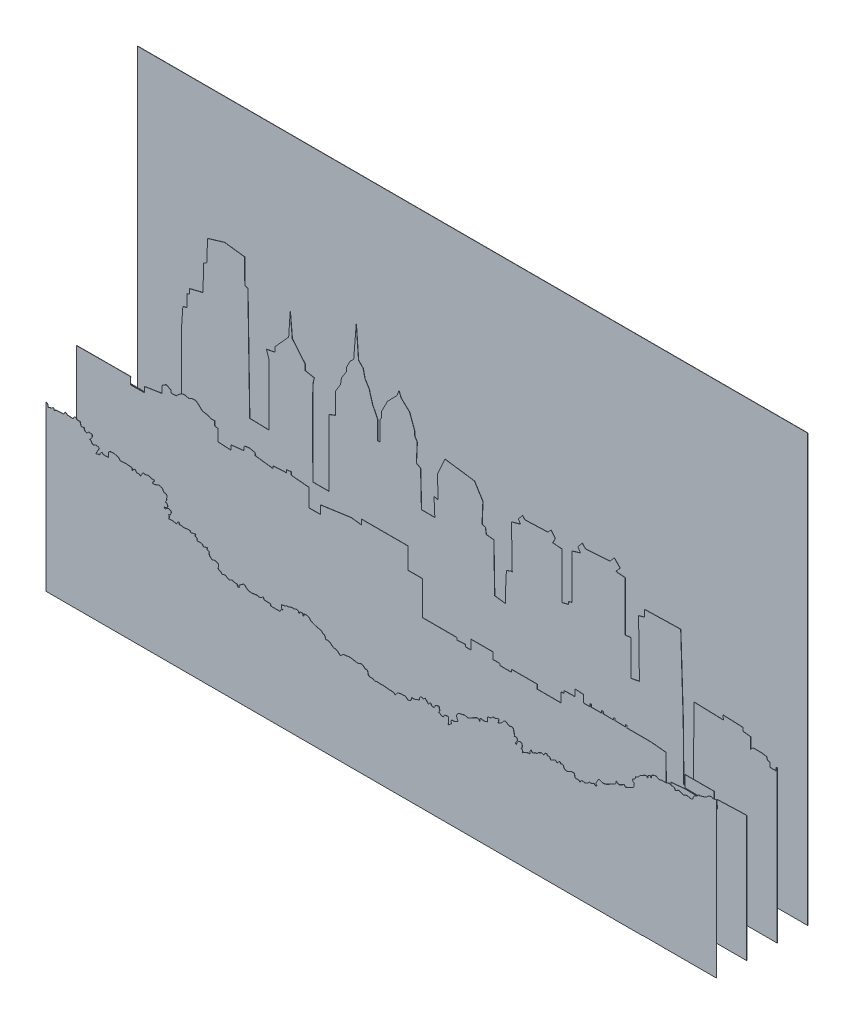
SolidWorks part; units mm, degrees
ref_plane "Front Plane" through (0, 0, 0) normal (0, 0, 1) x (1, 0, 0)
ref_plane "Top Plane" through (0, 0, 0) normal (0, 1, 0) x (1, 0, 0)
ref_plane "Right Plane" through (0, 0, 0) normal (1, 0, 0) x (0, 0, -1)
ref_plane "Plane2" through (0, 0, 12.7) normal (0, 0, 1) x (1, 0, 0)
ref_plane "Plane3" through (0, 0, 25.4) normal (0, 0, 1) x (1, 0, 0)
ref_plane "Plane4" through (0, 0, 38.1) normal (0, 0, 1) x (1, 0, 0)
sketch "Sketch2" plane through (0, 0, 12.7) normal (0, 0, 1) x (1, 0, 0)
  line L0 (279.4, -114.5341) -> (278.8098, -114.8294)
  line L1 (278.8098, -114.8294) -> (278.8098, -115.8829)
  line L2 (278.8098, -115.8829) -> (276.3531, -115.8829)
  line L3 (276.3531, -115.8829) -> (276.3531, -114.1271)
  line L4 (276.3531, -114.1271) -> (275.3003, -113.7759)
  line L5 (275.3003, -113.7759) -> (274.9493, -112.7224)
  line L6 (274.9493, -112.7224) -> (272.8436, -112.3712)
  line L7 (272.8436, -112.3712) -> (269.3341, -112.3712)
  line L8 (269.3341, -112.3712) -> (268.2813, -113.4247)
  line L9 (268.2813, -113.4247) -> (268.2813, -108.8596)
  line L10 (268.2813, -108.8596) -> (265.1227, -108.5084)
  line L11 (265.1227, -108.5084) -> (265.1227, -107.1038)
  line L12 (265.1227, -107.1038) -> (256.6999, -106.7526)
  line L13 (256.6999, -106.7526) -> (257.0508, -108.5084)
  line L14 (257.0508, -108.5084) -> (244.6514, -108.1264)
  line L15 (244.6514, -108.1264) -> (244.5456, -139.8764)
  line L16 (244.5456, -139.8764) -> (240.4181, -140.088)
  line L17 (240.4181, -140.088) -> (240.2053, -117.2875)
  line L18 (240.2053, -117.2875) -> (239.1524, -84.6293)
  line L19 (239.1524, -84.6293) -> (224.0616, -84.9805)
  line L20 (224.0616, -84.9805) -> (224.0616, -87.7898)
  line L21 (224.0616, -87.7898) -> (221.6049, -88.4921)
  line L22 (221.6049, -88.4921) -> (221.9559, -112.0201)
  line L23 (221.9559, -112.0201) -> (218.4463, -112.7224)
  line L24 (218.4463, -112.7224) -> (218.4463, -97.9735)
  line L25 (218.4463, -97.9735) -> (215.9897, -98.3247)
  line L26 (215.9897, -98.3247) -> (215.9897, -77.606)
  line L27 (215.9897, -77.606) -> (212.1293, -77.2549)
  line L28 (212.1293, -77.2549) -> (213.884, -75.1479)
  line L29 (213.884, -75.1479) -> (211.4274, -72.6897)
  line L30 (211.4274, -72.6897) -> (209.6726, -74.7967)
  line L31 (209.6726, -74.7967) -> (199.4951, -75.4991)
  line L32 (199.4951, -75.4991) -> (198.0913, -74.0944)
  line L33 (198.0913, -74.0944) -> (196.3365, -76.2014)
  line L34 (196.3365, -76.2014) -> (197.3894, -77.9572)
  line L35 (197.3894, -77.9572) -> (193.8799, -79.0107)
  line L36 (193.8799, -79.0107) -> (193.8799, -97.6224)
  line L37 (193.8799, -97.6224) -> (192.4761, -97.9735)
  line L38 (192.4761, -97.9735) -> (192.4761, -99.027)
  line L39 (192.4761, -99.027) -> (189.6685, -99.7294)
  line L40 (189.6685, -99.7294) -> (189.6685, -80.4153)
  line L41 (189.6685, -80.4153) -> (185.8081, -80.0642)
  line L42 (185.8081, -80.0642) -> (186.8609, -77.9572)
  line L43 (186.8609, -77.9572) -> (185.1061, -75.8502)
  line L44 (185.1061, -75.8502) -> (183.7023, -77.2549)
  line L45 (183.7023, -77.2549) -> (174.2267, -77.606)
  line L46 (174.2267, -77.606) -> (173.1738, -76.5525)
  line L47 (173.1738, -76.5525) -> (171.4191, -78.6595)
  line L48 (171.4191, -78.6595) -> (172.4719, -80.0642)
  line L49 (172.4719, -80.0642) -> (168.6115, -81.1177)
  line L50 (161.5925, -111.3178) -> (161.2415, -91.3014)
  line L51 (161.2415, -91.3014) -> (158.083, -90.9502)
  line L52 (158.083, -90.9502) -> (157.7321, -88.4921)
  line L53 (157.7321, -88.4921) -> (156.3282, -88.1409)
  line L54 (156.3282, -88.1409) -> (156.6792, -79.713)
  line L55 (156.6792, -79.713) -> (153.1697, -74.0944)
  line L56 (153.1697, -74.0944) -> (140.8864, -72.3386)
  line L57 (140.8864, -72.3386) -> (137.7279, -79.3618)
  line L58 (137.7279, -79.3618) -> (138.0788, -88.4921)
  line L59 (138.0788, -88.4921) -> (136.3241, -88.1409)
  line L60 (136.3241, -88.1409) -> (136.675, -95.5154)
  line L61 (136.675, -95.5154) -> (131.0598, -95.5154)
  line L62 (131.0598, -95.5154) -> (130.7089, -80.7665)
  line L63 (130.7089, -80.7665) -> (128.9541, -79.713)
  line L64 (128.9541, -79.713) -> (129.3051, -71.9874)
  line L65 (129.3051, -71.9874) -> (128.2522, -70.2316)
  line L66 (128.2522, -70.2316) -> (128.2522, -68.4758)
  line L67 (128.2522, -68.4758) -> (126.118, -62.7239)
  line L68 (126.118, -62.7239) -> (122.6255, -59.4431)
  line L69 (122.6255, -59.4431) -> (121.673, -57.2206)
  line L70 (121.673, -57.2206) -> (120.8823, -59.3455)
  line L71 (120.8823, -59.3455) -> (116.9105, -63.4647)
  line L72 (116.9105, -63.4647) -> (114.4764, -68.2272)
  line L73 (114.4764, -68.2272) -> (114.4764, -70.4497)
  line L74 (114.4764, -70.4497) -> (113.8633, -71.6363)
  line L75 (113.8633, -71.6363) -> (113.8633, -79.713)
  line L76 (113.8633, -79.713) -> (112.8104, -79.713)
  line L77 (112.8104, -79.713) -> (112.8104, -71.9874)
  line L78 (112.8104, -71.9874) -> (110.7047, -67.7734)
  line L79 (110.7047, -67.7734) -> (109.6519, -64.2618)
  line L80 (109.6519, -64.2618) -> (109.3009, -62.8571)
  line L81 (109.3009, -62.8571) -> (108.2481, -61.1013)
  line L82 (108.2481, -61.1013) -> (107.5462, -60.0479)
  line L83 (107.5462, -60.0479) -> (106.7505, -56.5855)
  line L84 (106.7505, -56.5855) -> (104.8456, -54.6806)
  line L85 (104.8456, -54.6806) -> (103.8931, -42.0864)
  line L86 (103.8931, -42.0864) -> (102.8347, -55.3156)
  line L87 (102.8347, -55.3156) -> (101.353, -56.6914)
  line L88 (101.353, -56.6914) -> (99.8253, -59.6967)
  line L89 (99.8253, -59.6967) -> (99.7655, -61.348)
  line L90 (99.7655, -61.348) -> (97.7196, -64.613)
  line L91 (97.7196, -64.613) -> (97.3686, -67.0711)
  line L92 (97.3686, -67.0711) -> (95.2629, -70.5828)
  line L93 (95.2629, -70.5828) -> (95.2629, -73.0409)
  line L94 (95.2629, -73.0409) -> (95.2629, -79.3618)
  line L95 (95.2629, -79.3618) -> (92.4554, -80.4153)
  line L96 (92.4554, -80.4153) -> (92.4554, -108.1573)
  line L97 (92.4554, -108.1573) -> (85.7873, -108.1573)
  line L98 (86.3247, -70.238) -> (82.6287, -69.5293)
  line L99 (82.6287, -69.5293) -> (82.6206, -67.1689)
  line L100 (82.6206, -67.1689) -> (77.223, -60.713)
  line L101 (77.223, -60.713) -> (76.3764, -51.188)
  line L102 (76.3764, -51.188) -> (75.7414, -60.8189)
  line L103 (75.7414, -60.8189) -> (70.0264, -67.1689)
  line L104 (70.0264, -67.1689) -> (69.9206, -69.1797)
  line L105 (69.9206, -69.1797) -> (66.4851, -69.8804)
  line L106 (66.4851, -69.8804) -> (67.5379, -73.0409)
  line L107 (59.4661, -98.3247) -> (58.7022, -51.7172)
  line L108 (58.7022, -51.7172) -> (57.4322, -51.3997)
  line L109 (57.4322, -51.3997) -> (57.3604, -41.085)
  line L110 (57.3604, -41.085) -> (48.9376, -40.0315)
  line L111 (48.9376, -40.0315) -> (41.9186, -42.1385)
  line L112 (41.9186, -42.1385) -> (41.5676, -51.2687)
  line L113 (41.5676, -51.2687) -> (40.1814, -51.823)
  line L114 (40.1814, -51.823) -> (40.0755, -62.6181)
  line L115 (40.0755, -62.6181) -> (34.4664, -63.9939)
  line L116 (34.4664, -63.9939) -> (34.4664, -66.0047)
  line L117 (34.4664, -66.0047) -> (33.3022, -66.4281)
  line L118 (33.3022, -66.4281) -> (33.4081, -71.4022)
  line L119 (33.4081, -71.4022) -> (31.6089, -71.8255)
  line L120 (31.6089, -71.8255) -> (31.0391, -80.0642)
  line L121 (31.0391, -80.0642) -> (31.0391, -110.9666)
  line L122 (31.0391, -110.9666) -> (0, -110.4702)
  line L123 (0, -110.4702) -> (0, -177.8007)
  line L124 (0, -177.8007) -> (279.4, -177.8007)
  line L125 (279.4, -177.8007) -> (279.4, -114.5341)
  spline S0 degree 2 poles (168.6115, -81.1177) (168.817, -97.9614) (168.9471, -98.9799) knots 50 50 50 51 51 51
  spline S3 degree 2 poles (168.9471, -98.9799) (168.7315, -98.8503) (166.5058, -99.7294) knots 53 53 53 54 54 54
  spline S4 degree 2 poles (166.5058, -99.7294) (165.8655, -111.1017) (166.1152, -111.9622) knots 54 54 54 55 55 55
  spline S7 degree 2 poles (166.1152, -111.9622) (165.5917, -111.7562) (161.5925, -111.3178) knots 57 57 57 58 58 58
  spline S8 degree 2 poles (85.7873, -108.1573) (85.6534, -74.3035) (85.7873, -73.0409) knots 106 106 106 107 107 107
  spline S9 degree 3 poles (85.7873, -73.0409) (85.9115, -71.8699) (86.436, -70.2546) (86.3247, -70.238) knots 107 107 107 107 108 108 108 108
  spline S10 degree 2 poles (67.5379, -73.0409) (67.5839, -96.8299) (67.5569, -98.5132) knots 117 117 117 118 118 118
  spline S11 degree 2 poles (67.5569, -98.5132) (67.5678, -98.5381) (59.4661, -98.3247) knots 118 118 118 119 119 119
sketch "Sketch3" plane through (0, 0, 25.4) normal (0, 0, 1) x (1, 0, 0)
  line L0 (279.4, -125.4381) -> (278.7297, -125.3772)
  line L1 (278.7297, -125.3772) -> (266.9822, -125.8005)
  line L2 (266.9822, -125.8005) -> (267.1939, -129.1872)
  line L3 (267.1939, -129.1872) -> (261.4789, -128.9755)
  line L4 (261.4789, -128.9755) -> (261.4789, -128.4464)
  line L5 (261.4789, -128.4464) -> (265.818, -128.3406)
  line L6 (265.818, -128.3406) -> (265.818, -123.4722)
  line L7 (265.818, -123.4722) -> (253.753, -123.4722)
  line L8 (253.753, -123.4722) -> (253.753, -128.2347)
  line L9 (253.753, -128.2347) -> (258.9389, -128.3406)
  line L10 (258.9389, -128.3406) -> (258.833, -128.7639)
  line L11 (258.833, -128.7639) -> (253.6472, -128.6581)
  line L12 (253.6472, -128.6581) -> (247.8264, -129.1872)
  line L13 (247.8264, -129.1872) -> (247.8264, -141.6755)
  line L14 (247.8264, -141.6755) -> (245.8155, -140.8289)
  line L15 (245.8155, -140.8289) -> (245.7097, -119.4505)
  line L16 (245.7097, -119.4505) -> (239.4655, -118.8156)
  line L17 (239.4655, -118.8156) -> (229.4113, -118.8156)
  line L18 (229.4113, -118.8156) -> (229.4113, -117.863)
  line L19 (229.4113, -117.863) -> (228.7763, -117.863)
  line L20 (228.7763, -117.863) -> (228.7763, -118.7097)
  line L21 (228.7763, -118.7097) -> (224.4372, -118.6039)
  line L22 (224.4372, -118.6039) -> (224.4372, -117.863)
  line L23 (224.4372, -117.863) -> (223.9081, -117.863)
  line L24 (223.9081, -117.863) -> (223.9081, -118.7097)
  line L25 (223.9081, -118.7097) -> (219.5689, -118.6039)
  line L26 (219.5689, -118.6039) -> (219.5689, -117.7572)
  line L27 (219.5689, -117.7572) -> (218.828, -117.7572)
  line L28 (218.828, -117.7572) -> (218.828, -118.7097)
  line L29 (218.828, -118.7097) -> (214.4889, -118.7097)
  line L30 (214.4889, -118.7097) -> (214.4889, -117.6514)
  line L31 (214.4889, -117.6514) -> (214.0655, -117.6514)
  line L32 (214.0655, -117.6514) -> (214.0655, -118.8156)
  line L33 (214.0655, -118.8156) -> (211.3138, -118.8156)
  line L34 (211.3138, -118.8156) -> (211.3138, -115.7464)
  line L35 (211.3138, -115.7464) -> (207.8214, -115.5347)
  line L36 (207.8214, -115.5347) -> (207.8214, -118.2864)
  line L37 (207.8214, -118.2864) -> (203.2706, -118.3922)
  line L38 (203.2706, -118.3922) -> (203.2706, -119.4505)
  line L39 (203.2706, -119.4505) -> (202.0005, -119.4505)
  line L40 (202.0005, -119.4505) -> (202.0005, -123.4722)
  line L41 (202.0005, -123.4722) -> (192.0522, -123.4722)
  line L42 (192.0522, -123.4722) -> (192.0522, -121.673)
  line L43 (192.0522, -121.673) -> (181.363, -121.673)
  line L44 (181.363, -121.673) -> (181.363, -122.7314)
  line L45 (181.363, -122.7314) -> (176.4947, -122.7314)
  line L46 (176.4947, -122.7314) -> (176.4947, -121.9906)
  line L47 (176.4947, -121.9906) -> (173.5314, -121.9906)
  line L48 (173.5314, -121.9906) -> (173.5314, -119.2389)
  line L49 (173.5314, -119.2389) -> (164.4297, -119.2389)
  line L50 (164.4297, -119.2389) -> (164.4297, -123.1547)
  line L51 (164.4297, -123.1547) -> (162.2072, -123.1547)
  line L52 (162.2072, -123.1547) -> (161.9956, -122.3081)
  line L53 (161.9956, -122.3081) -> (158.6089, -122.5197)
  line L54 (158.6089, -122.5197) -> (158.6089, -121.5672)
  line L55 (158.6089, -121.5672) -> (150.5655, -121.5672)
  line L56 (150.5655, -121.5672) -> (144.2155, -121.5672)
  line L57 (144.2155, -121.5672) -> (144.2155, -107.4914)
  line L58 (144.2155, -107.4914) -> (138.1831, -107.4914)
  line L59 (138.1831, -107.4914) -> (138.1831, -98.7072)
  line L60 (138.1831, -98.7072) -> (135.2197, -98.7072)
  line L61 (135.2197, -98.7072) -> (118.7097, -98.7072)
  line L62 (118.7097, -98.7072) -> (118.7097, -100.8239)
  line L63 (118.7097, -100.8239) -> (114.5822, -100.2947)
  line L64 (114.5822, -100.2947) -> (101.7764, -102.0939)
  line L65 (101.7764, -102.0939) -> (101.7764, -105.5864)
  line L66 (101.7764, -105.5864) -> (96.8022, -105.5864)
  line L67 (96.8022, -105.5864) -> (96.8022, -98.1781)
  line L68 (96.8022, -98.1781) -> (89.8172, -97.5431)
  line L69 (89.8172, -97.5431) -> (89.4997, -97.4372)
  line L70 (89.4997, -97.4372) -> (89.4997, -96.273)
  line L71 (89.4997, -96.273) -> (87.4889, -96.4847)
  line L72 (87.4889, -96.4847) -> (87.4889, -97.6489)
  line L73 (87.4889, -97.6489) -> (86.6422, -97.6489)
  line L74 (86.6422, -97.6489) -> (81.9855, -97.9664)
  line L75 (81.9855, -97.9664) -> (81.9855, -98.9189)
  line L76 (81.9855, -98.9189) -> (74.4714, -97.9664)
  line L77 (74.4714, -97.9664) -> (74.3655, -96.9081)
  line L78 (74.3655, -96.9081) -> (72.0372, -96.3789)
  line L79 (72.0372, -96.3789) -> (69.9206, -96.6964)
  line L80 (69.9206, -96.6964) -> (69.8147, -98.4956)
  line L81 (69.8147, -98.4956) -> (64.3113, -99.1306)
  line L82 (64.3113, -99.1306) -> (64.3113, -101.0355)
  line L83 (64.3113, -101.0355) -> (58.9139, -100.7181)
  line L84 (58.9139, -100.7181) -> (58.9139, -95.9556)
  line L85 (58.9139, -95.9556) -> (57.538, -95.638)
  line L86 (57.538, -95.638) -> (57.538, -93.8389)
  line L87 (57.538, -93.8389) -> (55.8447, -93.8389)
  line L88 (55.8447, -93.8389) -> (54.6805, -93.2039)
  line L89 (41.5572, -92.7806) -> (39.3347, -92.8864)
  line L90 (39.3347, -92.8864) -> (39.3347, -91.8281)
  line L91 (39.3347, -91.8281) -> (37.3239, -90.8755)
  line L92 (37.3239, -90.8755) -> (35.5247, -92.0397)
  line L93 (35.5247, -92.0397) -> (35.5247, -94.8972)
  line L94 (35.5247, -94.8972) -> (28.2222, -96.0614)
  line L95 (28.2222, -96.0614) -> (28.2222, -98.2839)
  line L96 (22.5072, -95.3206) -> (0, -95.4233)
  line L97 (0, -95.4233) -> (0, -177.8007)
  line L98 (0, -177.8007) -> (279.4, -177.8007)
  line L99 (279.4, -177.8007) -> (279.4, -125.4381)
  spline S0 degree 2 poles (54.6805, -93.2039) (53.3175, -93.1351) (52.4581, -92.7806) knots 89 89 89 90 90 90
  spline S1 degree 3 poles (52.4581, -92.7806) (51.5986, -92.426) (50.4766, -90.4502) (49.1772, -90.4522) knots 90 90 90 90 91 91 91 91
  spline S2 degree 2 poles (49.1772, -90.4522) (47.8778, -90.4542) (46.8489, -91.0872) knots 91 91 91 92 92 92
  spline S3 degree 2 poles (46.8489, -91.0872) (46.5744, -91.0746) (45.1555, -90.7697) knots 92 92 92 93 93 93
  spline S4 degree 2 poles (45.1555, -90.7697) (43.7367, -90.4648) (41.5572, -92.7806) knots 93 93 93 94 94 94
  spline S5 degree 2 poles (28.2222, -98.2839) (25.84, -98.3101) (22.4437, -98.3474) knots 101 101 101 102 102 102
  spline S6 degree 2 poles (22.4437, -98.3474) (22.3941, -97.9943) (22.5072, -95.3206) knots 102 102 102 103 103 103
sketch "Sketch4" plane through (0, 0, 38.1) normal (0, 0, 1) x (1, 0, 0)
  spline S0 degree 3 poles (277.6535, -113.4166) (277.8489, -113.5395) (278.1269, -113.5979) (278.3595, -113.579) (278.7103, -113.5503) (279.0536, -113.4293) (279.4, -113.3475) knots 344 344 344 344 345 345 345 346 346 346 346
  spline S1 degree 3 poles (275.0784, -114.5842) (275.7056, -114.1861) (276.092, -113.4532) (276.9622, -113.3634) (277.2245, -113.3364) (277.4013, -113.258) (277.6535, -113.4166) knots 342 342 342 342 343 343 343 344 344 344 344
  spline S2 degree 3 poles (274.832, -114.7215) (274.9201, -114.6961) (274.9989, -114.6346) (275.0784, -114.5842) knots 341 341 341 341 342 342 342 342
  spline S3 degree 3 poles (270.7793, -116.2787) (271.0483, -116.1877) (271.3769, -116.0603) (271.5159, -115.8445) (271.7585, -115.4676) (272.0293, -115.3147) (272.4622, -115.3515) (272.6253, -115.3654) (272.7982, -115.2898) (272.9637, -115.2444) (273.5874, -115.0735) (274.2107, -114.9007) (274.832, -114.7215) knots 337 337 337 337 338 338 338 339 339 339 340 340 340 341 341 341 341
  spline S4 degree 3 poles (269.4172, -118.1302) (269.6583, -117.9244) (269.7833, -117.5329) (269.8631, -117.199) (269.9868, -116.6819) (270.3079, -116.4381) (270.7793, -116.2787) knots 335 335 335 335 336 336 336 337 337 337 337
  spline S5 degree 3 poles (268.5118, -118.2598) (268.7894, -118.3381) (269.2171, -118.3009) (269.4172, -118.1302) knots 334 334 334 334 335 335 335 335
  spline S6 degree 3 poles (266.0554, -118.4191) (266.8481, -117.8055) (267.6618, -118.0199) (268.5118, -118.2598) knots 333 333 333 333 334 334 334 334
  spline S7 degree 3 poles (262.9789, -118.1896) (263.253, -118.0471) (263.5694, -117.78) (263.815, -117.8292) (264.4236, -117.9511) (264.9992, -118.2318) (265.5954, -118.4263) (265.7366, -118.4724) (265.9567, -118.4955) (266.0554, -118.4191) knots 330 330 330 330 331 331 331 332 332 332 333 333 333 333
  spline S8 degree 3 poles (262.3413, -118.5859) (262.5775, -118.4374) (262.7702, -118.2981) (262.9789, -118.1896) knots 329 329 329 329 330 330 330 330
  spline S9 degree 3 poles (260.8926, -117.5731) (261.6696, -117.4571) (262.0818, -117.8716) (262.3413, -118.5859) knots 328 328 328 328 329 329 329 329
  spline S10 degree 3 poles (260.4651, -117.4413) (260.6112, -117.4746) (260.7599, -117.5929) (260.8926, -117.5731) knots 327 327 327 327 328 328 328 328
  spline S11 degree 3 poles (259.6163, -117.2905) (259.8843, -117.2469) (260.1829, -117.3768) (260.4651, -117.4413) knots 326 326 326 326 327 327 327 327
  spline S12 degree 3 poles (256.445, -117.7031) (256.5179, -117.6462) (256.6827, -117.7132) (256.8047, -117.7118) (257.339, -117.7055) (257.8803, -117.7451) (258.4052, -117.6704) (258.8184, -117.6116) (259.2028, -117.3578) (259.6163, -117.2905) knots 323 323 323 323 324 324 324 325 325 325 326 326 326 326
  spline S13 degree 3 poles (254.4694, -117.5321) (255.0845, -117.7956) (255.7303, -118.2616) (256.445, -117.7031) knots 322 322 322 322 323 323 323 323
  spline S14 degree 3 poles (252.611, -117.9257) (252.8177, -117.7632) (253.1083, -117.7128) (253.3458, -117.5827) (253.7187, -117.3783) (254.0435, -117.3497) (254.4694, -117.5321) knots 320 320 320 320 321 321 321 322 322 322 322
  spline S15 degree 3 poles (252.4034, -118.446) (252.35, -118.3167) (252.4783, -118.0302) (252.611, -117.9257) knots 319 319 319 319 320 320 320 320
  spline S16 degree 3 poles (252.1662, -119.0873) (252.481, -118.9229) (252.5297, -118.7524) (252.4034, -118.446) knots 318 318 318 318 319 319 319 319
  spline S17 degree 3 poles (251.8468, -118.4123) (251.9592, -118.6497) (252.0578, -118.8582) (252.1662, -119.0873) knots 317 317 317 317 318 318 318 318
  spline S18 degree 3 poles (251.2681, -118.6778) (251.4583, -118.6085) (251.6376, -118.5095) (251.8468, -118.4123) knots 316 316 316 316 317 317 317 317
  spline S19 degree 3 poles (250.9507, -119.4467) (250.6904, -119.0283) (250.8748, -118.8212) (251.2681, -118.6778) knots 315 315 315 315 316 316 316 316
  spline S20 degree 3 poles (250.9241, -119.7554) (250.9355, -119.6509) (250.9943, -119.517) (250.9507, -119.4467) knots 314 314 314 314 315 315 315 315
  spline S21 degree 3 poles (250.6, -119.648) (250.6908, -119.7093) (250.8149, -119.7213) (250.9241, -119.7554) knots 313 313 313 313 314 314 314 314
  spline S22 degree 3 poles (249.1495, -119.643) (249.4659, -119.4838) (249.8121, -119.353) (250.1589, -119.3012) (250.2845, -119.2824) (250.441, -119.5406) (250.6, -119.648) knots 311 311 311 311 312 312 312 313 313 313 313
  spline S23 degree 3 poles (248.277, -120.2105) (248.5931, -120.0869) (248.8411, -119.7982) (249.1495, -119.643) knots 310 310 310 310 311 311 311 311
  spline S24 degree 3 poles (247.0043, -121.2797) (247.2666, -120.7246) (247.7198, -120.4283) (248.277, -120.2105) knots 309 309 309 309 310 310 310 310
  spline S25 degree 3 poles (245.6518, -121.9401) (246.0428, -121.7742) (246.4105, -121.6234) (246.7729, -121.4608) (246.8609, -121.4213) (246.9666, -121.3595) (247.0043, -121.2797) knots 307 307 307 307 308 308 308 309 309 309 309
  spline S26 degree 3 poles (244.8082, -123.1288) (245.3596, -122.9278) (245.7205, -122.584) (245.6518, -121.9401) knots 306 306 306 306 307 307 307 307
  spline S27 degree 3 poles (244.813, -124.2751) (244.6928, -124.1824) (244.6668, -123.9741) (244.5822, -123.827) (244.3974, -123.5058) (244.4325, -123.2658) (244.8082, -123.1288) knots 304 304 304 304 305 305 305 306 306 306 306
  spline S28 degree 3 poles (245.4544, -124.6041) (245.2673, -124.5125) (245.0128, -124.4292) (244.813, -124.2751) knots 303 303 303 303 304 304 304 304
  spline S29 degree 3 poles (244.8273, -126.1757) (244.9105, -126.1336) (245, -125.998) (244.9969, -125.909) (244.9772, -125.3441) (245.0335, -124.8208) (245.4544, -124.6041) knots 301 301 301 301 302 302 302 303 303 303 303
  spline S30 degree 3 poles (241.2193, -127.42) (241.3384, -127.8726) (241.6147, -127.7636) (241.8846, -127.633) (242.8698, -127.1561) (243.8509, -126.6704) (244.8273, -126.1757) knots 299 299 299 299 300 300 300 301 301 301 301
  spline S31 degree 3 poles (240.9015, -127.1409) (241.0029, -127.2255) (241.1884, -127.3024) (241.2193, -127.42) knots 298 298 298 298 299 299 299 299
  spline S32 degree 3 poles (239.018, -128.1348) (239.6711, -127.8682) (240.2755, -127.4824) (240.9015, -127.1409) knots 297 297 297 297 298 298 298 298
  spline S33 degree 3 poles (238.211, -127.876) (238.4786, -127.9842) (238.8168, -128.217) (239.018, -128.1348) knots 296 296 296 296 297 297 297 297
  spline S34 degree 3 poles (237.5604, -127.5373) (237.8561, -127.6932) (238.0267, -127.8014) (238.211, -127.876) knots 295 295 295 295 296 296 296 296
  spline S35 degree 3 poles (236.8231, -128.9905) (237.399, -128.8532) (237.7507, -128.3385) (237.5604, -127.5373) knots 294 294 294 294 295 295 295 295
  spline S36 degree 3 poles (233.3709, -130.7444) (233.7902, -130.5983) (234.1883, -130.3532) (234.5734, -130.1692) (235.3349, -129.8053) (235.9588, -129.1966) (236.8231, -128.9905) knots 292 292 292 292 293 293 293 294 294 294 294
  spline S37 degree 3 poles (231.4864, -130.8083) (232.1228, -131.0503) (232.7575, -130.9582) (233.3709, -130.7444) knots 291 291 291 291 292 292 292 292
  spline S38 degree 3 poles (230.68, -130.4997) (230.9555, -130.5793) (231.2172, -130.7059) (231.4864, -130.8083) knots 290 290 290 290 291 291 291 291
  spline S39 degree 3 poles (230.0889, -130.8779) (230.2223, -130.6235) (230.3599, -130.4072) (230.68, -130.4997) knots 289 289 289 289 290 290 290 290
  spline S40 degree 3 poles (229.1706, -132.5056) (229.508, -131.912) (229.8135, -131.4028) (230.0889, -130.8779) knots 288 288 288 288 289 289 289 289
  spline S41 degree 3 poles (229.6523, -133.2341) (229.4398, -132.9127) (229.2747, -132.6631) (229.1706, -132.5056) knots 287 287 287 287 288 288 288 288
  spline S42 degree 3 poles (228.8707, -133.5326) (229.1392, -133.4301) (229.4104, -133.3265) (229.6523, -133.2341) knots 286 286 286 286 287 287 287 287
  spline S43 degree 3 poles (226.7528, -133.4715) (227.1672, -133.6316) (227.4869, -133.4509) (227.8078, -133.2446) (228.363, -132.8878) (228.5286, -132.928) (228.8707, -133.5326) knots 284 284 284 284 285 285 285 286 286 286 286
  spline S44 degree 3 poles (226.3151, -133.5144) (226.3271, -133.4644) (226.6248, -133.4221) (226.7528, -133.4715) knots 283 283 283 283 284 284 284 284
  spline S45 degree 3 poles (225.041, -134.4994) (225.4742, -134.1934) (226.1533, -134.1901) (226.3151, -133.5144) knots 282 282 282 282 283 283 283 283
  spline S46 degree 3 poles (222.5676, -135.4002) (223.2255, -134.3727) (223.0714, -134.4287) (224.2952, -134.607) (224.5381, -134.6424) (224.8564, -134.6298) (225.041, -134.4994) knots 280 280 280 280 281 281 281 282 282 282 282
  spline S47 degree 3 poles (222.06, -135.0287) (222.2409, -135.1288) (222.3974, -135.2729) (222.5676, -135.4002) knots 279 279 279 279 280 280 280 280
  spline S48 degree 3 poles (221.5471, -134.8559) (221.646, -134.7942) (221.8994, -134.9397) (222.06, -135.0287) knots 278 278 278 278 279 279 279 279
  spline S49 degree 3 poles (220.499, -134.7876) (220.7008, -134.9685) (221.0718, -135.152) (221.5471, -134.8559) knots 277 277 277 277 278 278 278 278
  spline S50 degree 3 poles (220.0677, -133.3895) (220.2455, -133.792) (220.3385, -134.2321) (220.499, -134.7876) knots 276 276 276 276 277 277 277 277
  spline S51 degree 3 poles (218.7104, -133.4714) (218.9427, -133.3749) (219.2183, -133.3697) (219.4763, -133.3521) (219.68, -133.3382) (220.0303, -133.3048) (220.0677, -133.3895) knots 274 274 274 274 275 275 275 276 276 276 276
  spline S52 degree 3 poles (215.8081, -133.4785) (215.8534, -133.6598) (216.0616, -133.8455) (216.2416, -133.937) (216.4972, -134.0671) (216.7921, -134.1395) (217.0783, -134.1818) (217.2314, -134.2044) (217.414, -134.138) (217.5613, -134.0664) (217.9493, -133.8777) (218.3136, -133.6362) (218.7104, -133.4714) knots 270 270 270 270 271 271 271 272 272 272 273 273 273 274 274 274 274
  spline S53 degree 3 poles (214.5018, -132.8058) (215.274, -132.4315) (215.5875, -132.5959) (215.8081, -133.4785) knots 269 269 269 269 270 270 270 270
  spline S54 degree 3 poles (214.2119, -132.1961) (214.3086, -132.3994) (214.4053, -132.6028) (214.5018, -132.8058) knots 268 268 268 268 269 269 269 269
  spline S55 degree 3 poles (213.4819, -132.6879) (213.6991, -132.4946) (213.9661, -132.3573) (214.2119, -132.1961) knots 267 267 267 267 268 268 268 268
  spline S56 degree 3 poles (213.1194, -133.25) (213.2571, -133.0289) (213.3345, -132.8192) (213.4819, -132.6879) knots 266 266 266 266 267 267 267 267
  spline S57 degree 3 poles (210.2547, -133.56) (210.642, -133.3794) (211.0618, -133.2508) (211.4012, -133.0092) (211.8822, -132.6669) (212.389, -132.6232) (212.8181, -132.9985) (212.9105, -133.0793) (213.0066, -133.156) (213.1194, -133.25) knots 263 263 263 263 264 264 264 265 265 265 266 266 266 266
  spline S58 degree 3 poles (209.0434, -132.7656) (209.7372, -132.4177) (210.0428, -132.5962) (210.2547, -133.56) knots 262 262 262 262 263 263 263 263
  spline S59 degree 3 poles (207.7564, -132.648) (207.9424, -132.2832) (208.2435, -132.0391) (208.6142, -132.1227) (208.7944, -132.1634) (208.8998, -132.5362) (209.0434, -132.7656) knots 260 260 260 260 261 261 261 262 262 262 262
  spline S60 degree 3 poles (206.5407, -132.8531) (206.8202, -132.951) (207.0893, -133.1131) (207.357, -133.1109) (207.4938, -133.1098) (207.6627, -132.8318) (207.7564, -132.648) knots 258 258 258 258 259 259 259 260 260 260 260
  spline S61 degree 3 poles (205.2076, -133.4614) (205.6697, -133.2258) (206.1511, -133.028) (206.5407, -132.8531) knots 257 257 257 257 258 258 258 258
  spline S62 degree 3 poles (204.7905, -133.8547) (204.9262, -133.7189) (205.0442, -133.5448) (205.2076, -133.4614) knots 256 256 256 256 257 257 257 257
  spline S63 degree 3 poles (204.4728, -134.1745) (204.5389, -134.1951) (204.6804, -133.9649) (204.7905, -133.8547) knots 255 255 255 255 256 256 256 256
  spline S64 degree 3 poles (202.6393, -134.7261) (202.7179, -134.7195) (202.7732, -134.7254) (202.8212, -134.7093) (203.3666, -134.5263) (203.7842, -133.9602) (204.4728, -134.1745) knots 253 253 253 253 254 254 254 255 255 255 255
  spline S65 degree 3 poles (202.1758, -134.0864) (202.3332, -134.3036) (202.4905, -134.5208) (202.6393, -134.7261) knots 252 252 252 252 253 253 253 253
  spline S66 degree 3 poles (201.9122, -134.1776) (202.0001, -134.1472) (202.0879, -134.1168) (202.1758, -134.0864) knots 251 251 251 251 252 252 252 252
  spline S67 degree 3 poles (201.6273, -135.678) (201.733, -135.1214) (201.8226, -134.6495) (201.9122, -134.1776) knots 250 250 250 250 251 251 251 251
  spline S68 degree 3 poles (198.6661, -136.7434) (199.6719, -136.1637) (200.5803, -135.5789) (201.6273, -135.678) knots 249 249 249 249 250 250 250 250
  spline S69 degree 3 poles (198.1834, -135.5265) (198.5797, -135.8428) (198.6785, -136.1837) (198.6661, -136.7434) knots 248 248 248 248 249 249 249 249
  spline S70 degree 3 poles (198.5747, -134.9513) (198.2962, -135.1058) (197.8023, -135.2225) (198.1834, -135.5265) knots 247 247 247 247 248 248 248 248
  spline S71 degree 3 poles (198.3018, -133.5539) (198.4236, -134.0161) (198.4906, -134.4926) (198.5747, -134.9513) knots 246 246 246 246 247 247 247 247
  spline S72 degree 3 poles (196.4707, -134.1087) (196.7717, -133.5357) (197.2741, -133.2659) (197.9102, -133.3596) (198.0523, -133.3805) (198.2768, -133.4592) (198.3018, -133.5539) knots 244 244 244 244 245 245 245 246 246 246 246
  spline S73 degree 3 poles (195.9131, -135.1933) (196.1432, -134.7452) (196.3042, -134.4255) (196.4707, -134.1087) knots 243 243 243 243 244 244 244 244
  spline S74 degree 3 poles (195.5597, -134.4804) (195.6568, -134.6764) (195.754, -134.8723) (195.9131, -135.1933) knots 242 242 242 242 243 243 243 243
  spline S75 degree 3 poles (195.7285, -134.5288) (195.6722, -134.5126) (195.6159, -134.4965) (195.5597, -134.4804) knots 241 241 241 241 242 242 242 242
  spline S76 degree 3 poles (196.4666, -133.2304) (196.4872, -133.6501) (195.9931, -134.095) (195.7285, -134.5288) knots 240 240 240 240 241 241 241 241
  spline S77 degree 3 poles (195.1369, -132.5431) (195.8711, -132.3475) (196.438, -132.6492) (196.4666, -133.2304) knots 239 239 239 239 240 240 240 240
  spline S78 degree 3 poles (195.2235, -132.0361) (195.2396, -132.1728) (195.1784, -132.3185) (195.1369, -132.5431) knots 238 238 238 238 239 239 239 239
  spline S79 degree 3 poles (195.0516, -131.139) (195.1221, -131.4352) (195.188, -131.7343) (195.2235, -132.0361) knots 237 237 237 237 238 238 238 238
  spline S80 degree 3 poles (193.4382, -129.825) (194.2949, -129.4283) (194.882, -129.7856) (194.8964, -130.7156) (194.8986, -130.8572) (195.0169, -130.9932) (195.0516, -131.139) knots 235 235 235 235 236 236 236 237 237 237 237
  spline S81 degree 3 poles (191.5507, -129.0682) (192.0385, -129.3063) (192.5036, -129.5912) (192.9923, -129.8274) (193.1144, -129.8864) (193.3131, -129.8829) (193.4382, -129.825) knots 233 233 233 233 234 234 234 235 235 235 235
  spline S82 degree 3 poles (190.4856, -129.5873) (190.6697, -129.3051) (191.2987, -128.9451) (191.5507, -129.0682) knots 232 232 232 232 233 233 233 233
  spline S83 degree 3 poles (188.9731, -130.8185) (189.6772, -130.6491) (190.1156, -130.1543) (190.4856, -129.5873) knots 231 231 231 231 232 232 232 232
  spline S84 degree 3 poles (188.3981, -131.0995) (188.702, -130.9482) (188.8303, -130.8529) (188.9731, -130.8185) knots 230 230 230 230 231 231 231 231
  spline S85 degree 3 poles (188.6845, -130.0298) (188.6045, -130.3439) (188.5174, -130.6562) (188.3981, -131.0995) knots 229 229 229 229 230 230 230 230
  spline S86 degree 3 poles (188.738, -129.6696) (188.7898, -129.7347) (188.7155, -129.9079) (188.6845, -130.0298) knots 228 228 228 228 229 229 229 229
  spline S87 degree 3 poles (187.4333, -129.9575) (187.7476, -129.8267) (188.0515, -129.6671) (188.3733, -129.561) (188.4778, -129.5265) (188.6709, -129.5853) (188.738, -129.6696) knots 226 226 226 226 227 227 227 228 228 228 228
  spline S88 degree 3 poles (185.544, -130.6982) (185.9797, -130.2438) (186.3801, -129.872) (187.0676, -130.0616) (187.1724, -130.0905) (187.3153, -130.0066) (187.4333, -129.9575) knots 224 224 224 224 225 225 225 226 226 226 226
  spline S89 degree 3 poles (184.0252, -131.1438) (184.1706, -131.1132) (184.3902, -131.0794) (184.6023, -131.0194) (184.9255, -130.9282) (185.3398, -130.9111) (185.544, -130.6982) knots 222 222 222 222 223 223 223 224 224 224 224
  spline S90 degree 3 poles (184.0252, -132.9889) (184.0252, -132.3912) (184.0252, -131.7935) (184.0252, -131.1438) knots 221 221 221 221 222 222 222 222
  spline S91 degree 3 poles (183.8562, -132.8978) (183.9125, -132.9281) (183.9689, -132.9585) (184.0252, -132.9889) knots 220 220 220 220 221 221 221 221
  spline S92 degree 3 poles (180.8439, -134.3311) (180.8527, -134.1732) (180.8678, -134.0076) (180.8701, -133.8419) (180.8795, -133.1489) (180.9944, -133.0818) (181.7004, -133.2293) (182.0883, -133.3103) (182.5038, -133.3753) (182.8886, -133.3202) (183.2244, -133.2721) (183.5346, -133.0455) (183.8562, -132.8978) knots 216 216 216 216 217 217 217 218 218 218 219 219 219 220 220 220 220
  spline S93 degree 3 poles (180.6853, -134.3294) (180.6935, -134.3428) (180.7425, -134.3311) (180.8439, -134.3311) knots 215 215 215 215 216 216 216 216
  spline S94 degree 3 poles (178.9153, -133.9836) (179.939, -133.4902) (180.2229, -133.5778) (180.6853, -134.3294) knots 214 214 214 214 215 215 215 215
  spline S95 degree 3 poles (174.5015, -135.2586) (174.8178, -135.3466) (175.2278, -135.483) (175.6484, -135.5662) (175.8063, -135.5975) (176.0081, -135.5421) (176.1569, -135.4636) (177.08, -134.9769) (177.9762, -134.4361) (178.9153, -133.9836) knots 211 211 211 211 212 212 212 213 213 213 214 214 214 214
  spline S96 degree 3 poles (171.1237, -137.1478) (171.2163, -136.3413) (171.9785, -135.7885) (172.7972, -135.6698) (173.3545, -135.589) (173.8972, -135.4082) (174.5015, -135.2586) knots 209 209 209 209 210 210 210 211 211 211 211
  spline S97 degree 3 poles (171.5099, -138.3191) (171.3616, -137.9311) (171.0811, -137.519) (171.1237, -137.1478) knots 208 208 208 208 209 209 209 209
  spline S98 degree 3 poles (171.7798, -138.9034) (171.7065, -138.7466) (171.5937, -138.5384) (171.5099, -138.3191) knots 207 207 207 207 208 208 208 208
  spline S99 degree 3 poles (168.7111, -141.3608) (169.0413, -141.1582) (169.033, -140.9917) (168.8991, -140.6905) (168.6338, -140.0937) (168.9211, -139.6854) (169.563, -139.7011) (169.7646, -139.706) (169.9919, -139.759) (170.1635, -139.6863) (170.6959, -139.4608) (171.2072, -139.1855) (171.7798, -138.9034) knots 203 203 203 203 204 204 204 205 205 205 206 206 206 207 207 207 207
  spline S100 degree 3 poles (167.7942, -142.2112) (168.0964, -141.9221) (168.3626, -141.5745) (168.7111, -141.3608) knots 202 202 202 202 203 203 203 203
  spline S101 degree 3 poles (167.6361, -142.1109) (167.6888, -142.1444) (167.7415, -142.1778) (167.7942, -142.2112) knots 201 201 201 201 202 202 202 202
  spline S102 degree 3 poles (167.7695, -139.1571) (167.7236, -140.1744) (167.6798, -141.1427) (167.6361, -142.1109) knots 200 200 200 200 201 201 201 201
  spline S103 degree 3 poles (165.9513, -139.7619) (166.0039, -139.6285) (166.0855, -139.4266) (166.1856, -139.4052) (166.6824, -139.2988) (167.1899, -139.2423) (167.7695, -139.1571) knots 198 198 198 198 199 199 199 200 200 200 200
  spline S104 degree 3 poles (164.4724, -140.0709) (165.127, -140.5531) (165.6463, -140.5354) (165.9513, -139.7619) knots 197 197 197 197 198 198 198 198
  spline S105 degree 3 poles (163.6283, -139.6827) (163.943, -139.8234) (164.2417, -139.901) (164.4724, -140.0709) knots 196 196 196 196 197 197 197 197
  spline S106 degree 3 poles (163.863, -138.0713) (163.9659, -138.5435) (164.3187, -139.0293) (163.7173, -139.4336) (163.6432, -139.4834) (163.6417, -139.6413) (163.6283, -139.6827) knots 194 194 194 194 195 195 195 196 196 196 196
  spline S107 degree 3 poles (163.7952, -137.3155) (163.8236, -137.6553) (163.8189, -137.8687) (163.863, -138.0713) knots 193 193 193 193 194 194 194 194
  spline S108 degree 3 poles (161.6222, -138.8745) (161.8153, -138.8523) (162.085, -138.4834) (162.1116, -138.2481) (162.1597, -137.8228) (162.3815, -137.7311) (162.7224, -137.6869) (162.8357, -137.6721) (162.9419, -137.6062) (163.0527, -137.5678) (163.2904, -137.4855) (163.529, -137.4058) (163.7952, -137.3155) knots 189 189 189 189 190 190 190 191 191 191 192 192 192 193 193 193 193
  spline S109 degree 3 poles (160.4889, -138.4026) (160.705, -138.8549) (161.2061, -138.9224) (161.6222, -138.8745) knots 188 188 188 188 189 189 189 189
  spline S110 degree 3 poles (159.8143, -138.3709) (160.053, -138.0457) (160.2476, -137.8976) (160.4889, -138.4026) knots 187 187 187 187 188 188 188 188
  spline S111 degree 3 poles (159.4573, -138.8693) (159.5531, -138.7353) (159.6816, -138.5516) (159.8143, -138.3709) knots 186 186 186 186 187 187 187 187
  spline S112 degree 3 poles (157.9491, -137.4012) (158.4717, -137.9099) (158.9761, -138.4008) (159.4573, -138.8693) knots 185 185 185 185 186 186 186 186
  spline S113 degree 3 poles (157.32, -138.1219) (157.5035, -137.9117) (157.6932, -137.6943) (157.9491, -137.4012) knots 184 184 184 184 185 185 185 185
  spline S114 degree 3 poles (155.6866, -138.8506) (155.692, -138.6638) (155.7025, -138.4639) (155.7714, -138.2947) (156.0083, -137.7126) (156.3775, -137.6288) (157.32, -138.1219) knots 182 182 182 182 183 183 183 184 184 184 184
  spline S115 degree 3 poles (152.4452, -139.9188) (153.4193, -140.2072) (154.252, -139.8246) (155.0724, -139.391) (155.1006, -139.3761) (155.1427, -139.3812) (155.1771, -139.3858) (155.5947, -139.4418) (155.6766, -139.1913) (155.6866, -138.8506) knots 179 179 179 179 180 180 180 181 181 181 182 182 182 182
  spline S116 degree 3 poles (152.0199, -141.119) (152.4956, -140.8925) (152.3783, -140.4364) (152.4452, -139.9188) knots 178 178 178 178 179 179 179 179
  spline S117 degree 3 poles (146.5357, -141.2069) (147.015, -140.9795) (147.5964, -140.9547) (148.1392, -140.8785) (148.436, -140.8369) (148.7622, -140.9328) (149.0407, -140.8503) (149.4946, -140.716) (149.8315, -140.8134) (150.177, -141.1135) (150.4202, -141.3248) (150.7344, -141.6151) (151.0007, -141.5993) (151.3485, -141.5786) (151.6766, -141.2824) (152.0199, -141.119) knots 173 173 173 173 174 174 174 175 175 175 176 176 176 177 177 177 178 178 178 178
  spline S118 degree 3 poles (145.7748, -142.1533) (146.0079, -141.8163) (146.2058, -141.3634) (146.5357, -141.2069) knots 172 172 172 172 173 173 173 173
  spline S119 degree 3 poles (136.3623, -141.3371) (136.7735, -141.8) (137.1853, -141.7535) (137.6697, -141.524) (137.7865, -141.4686) (137.9494, -141.52) (138.0875, -141.4988) (138.8174, -141.387) (139.5452, -141.8078) (140.2768, -141.5057) (140.3347, -141.4818) (140.4153, -141.5097) (140.4849, -141.5179) (141.3271, -141.6177) (142.1675, -141.7372) (143.0119, -141.8112) (143.4845, -141.8526) (143.9671, -141.7848) (144.4384, -141.8327) (144.6814, -141.8574) (145.0144, -141.9642) (145.1235, -142.1446) (145.3834, -142.5748) (145.5386, -142.4947) (145.7748, -142.1533) knots 164 164 164 164 165 165 165 166 166 166 167 167 167 168 168 168 169 169 169 170 170 170 171 171 171 172 172 172 172
  spline S120 degree 3 poles (125.3025, -138.5224) (126.3801, -138.0534) (127.4275, -138.4392) (128.4877, -138.5907) (129.1638, -138.6872) (129.8396, -138.9391) (130.5279, -138.5743) (131.3589, -138.134) (132.0441, -138.3169) (132.667, -139.0551) (132.7903, -139.2012) (133.0862, -139.3962) (133.1723, -139.3459) (133.5815, -139.1066) (133.8391, -139.3852) (133.9924, -139.6168) (134.1612, -139.872) (134.1703, -140.2329) (134.2481, -140.548) (134.2652, -140.6174) (134.2604, -140.6992) (134.2964, -140.7556) (134.6336, -141.2847) (134.9873, -141.3959) (135.6435, -141.2687) (135.8776, -141.2234) (136.2433, -141.2031) (136.3623, -141.3371) knots 155 155 155 155 156 156 156 157 157 157 158 158 158 159 159 159 160 160 160 161 161 161 162 162 162 163 163 163 164 164 164 164
  spline S121 degree 3 poles (123.1106, -139.3426) (123.5542, -138.8739) (124.0484, -138.4508) (124.7777, -138.5345) (124.9514, -138.5544) (125.1534, -138.5873) (125.3025, -138.5224) knots 153 153 153 153 154 154 154 155 155 155 155
  spline S122 degree 3 poles (122.2463, -139.3704) (122.6959, -139.7733) (122.6723, -139.8055) (123.1106, -139.3426) knots 152 152 152 152 153 153 153 153
  spline S123 degree 3 poles (119.264, -137.9119) (119.5369, -138.159) (119.7111, -138.3914) (120.0745, -138.3213) (121.0637, -138.1305) (121.6377, -138.8252) (122.2463, -139.3704) knots 150 150 150 150 151 151 151 152 152 152 152
  spline S124 degree 3 poles (116.4079, -136.8999) (116.5068, -136.9241) (116.5546, -136.9408) (116.6036, -136.9465) (116.6558, -136.9526) (116.7148, -136.9634) (116.7614, -136.9463) (117.8704, -136.54) (118.5871, -137.299) (119.264, -137.9119) knots 147 147 147 147 148 148 148 149 149 149 150 150 150 150
  spline S125 degree 3 poles (111.059, -133.6586) (111.5362, -133.8733) (112.0455, -134.0174) (112.5429, -134.1862) (112.7825, -134.2676) (113.0222, -134.3584) (113.2694, -134.4061) (114.0057, -134.5481) (114.8616, -134.4091) (115.2664, -135.297) (115.2832, -135.3338) (115.3509, -135.3533) (115.3987, -135.3689) (116.1393, -135.6116) (116.5709, -136.0675) (116.4079, -136.8999) knots 142 142 142 142 143 143 143 144 144 144 145 145 145 146 146 146 147 147 147 147
  spline S126 degree 3 poles (107.5484, -132.205) (108.5115, -132.1788) (109.453, -131.9789) (110.0741, -133.0148) (110.2566, -133.3193) (110.7009, -133.4975) (111.059, -133.6586) knots 140 140 140 140 141 141 141 142 142 142 142
  spline S127 degree 3 poles (107.5139, -132.9936) (107.5263, -132.7092) (107.5369, -132.4688) (107.5484, -132.205) knots 139 139 139 139 140 140 140 140
  spline S128 degree 3 poles (107.0299, -133.0462) (107.2199, -133.0256) (107.3673, -133.0095) (107.5139, -132.9936) knots 138 138 138 138 139 139 139 139
  spline S129 degree 3 poles (106.969, -132.2936) (106.9919, -132.5762) (107.0097, -132.7965) (107.0299, -133.0462) knots 137 137 137 137 138 138 138 138
  spline S130 degree 3 poles (105.4555, -133.0901) (105.5468, -132.9827) (105.708, -132.8805) (105.7166, -132.7669) (105.7455, -132.3828) (105.927, -132.2527) (106.2931, -132.2895) (106.5141, -132.3118) (106.7392, -132.2936) (106.969, -132.2936) knots 134 134 134 134 135 135 135 136 136 136 137 137 137 137
  spline S131 degree 3 poles (105.3251, -132.9996) (105.3686, -133.0298) (105.412, -133.0599) (105.4555, -133.0901) knots 133 133 133 133 134 134 134 134
  spline S132 degree 3 poles (105.2865, -132.4859) (105.2994, -132.6573) (105.3122, -132.8285) (105.3251, -132.9996) knots 132 132 132 132 133 133 133 133
  spline S133 degree 3 poles (98.1522, -133.5919) (98.7825, -133.375) (99.5794, -133.6053) (100.0711, -132.9509) (100.0864, -132.9305) (100.1408, -132.9256) (100.1722, -132.9332) (101.0396, -133.1449) (101.7309, -132.4883) (102.5479, -132.4527) (102.9326, -132.436) (103.3931, -132.5418) (103.6859, -132.3678) (104.2942, -132.0061) (104.7738, -132.1851) (105.2865, -132.4859) knots 127 127 127 127 128 128 128 129 129 129 130 130 130 131 131 131 132 132 132 132
  spline S134 degree 3 poles (98.7917, -135.1563) (98.0905, -134.8303) (98.0311, -134.6754) (98.1522, -133.5919) knots 126 126 126 126 127 127 127 127
  spline S135 degree 3 poles (97.7714, -135.8765) (97.8239, -135.4074) (98.0567, -135.2396) (98.4941, -135.252) (98.5763, -135.2544) (98.6601, -135.2005) (98.7917, -135.1563) knots 124 124 124 124 125 125 125 126 126 126 126
  spline S136 degree 3 poles (93.5823, -136.3144) (94.8753, -136.3144) (96.1191, -136.3289) (97.3617, -136.2952) (97.5085, -136.2913) (97.7536, -136.0358) (97.7714, -135.8765) knots 122 122 122 122 123 123 123 124 124 124 124
  spline S137 degree 3 poles (90.8427, -135.4228) (91.5328, -135.4748) (92.1958, -135.5772) (92.8554, -135.5583) (93.41, -135.5423) (93.6511, -135.6993) (93.5634, -136.2643) (93.557, -136.3051) (93.5994, -136.3534) (93.5823, -136.3144) knots 119 119 119 119 120 120 120 121 121 121 122 122 122 122
  spline S138 degree 3 poles (90.7805, -135.2094) (90.8122, -135.2854) (90.8271, -135.3683) (90.8427, -135.4228) knots 118 118 118 118 119 119 119 119
  spline S139 degree 3 poles (80.4521, -135.3516) (80.9887, -134.9643) (81.4669, -134.6466) (81.9127, -134.2887) (82.2693, -134.0024) (82.7202, -134.0263) (83.003, -134.3705) (83.4866, -134.9589) (84.0235, -135.427) (84.8597, -135.4887) (85.3638, -135.5259) (85.8212, -135.6777) (86.3594, -135.4968) (86.919, -135.3086) (87.5501, -135.3318) (88.1506, -135.269) (88.2118, -135.2626) (88.283, -135.2894) (88.3404, -135.3187) (88.8052, -135.5563) (89.547, -135.4216) (89.8887, -135.0334) (90.3861, -134.4684) (90.4794, -134.4863) (90.7805, -135.2094) knots 110 110 110 110 111 111 111 112 112 112 113 113 113 114 114 114 115 115 115 116 116 116 117 117 117 118 118 118 118
  spline S140 degree 3 poles (80.5932, -136.1914) (80.5373, -135.8586) (80.4839, -135.5408) (80.4521, -135.3516) knots 109 109 109 109 110 110 110 110
  spline S141 degree 3 poles (79.7205, -136.1914) (80.0307, -136.1914) (80.3083, -136.1914) (80.5932, -136.1914) knots 108 108 108 108 109 109 109 109
  spline S142 degree 3 poles (79.6617, -135.3628) (79.6833, -135.6669) (79.7014, -135.9217) (79.7205, -136.1914) knots 107 107 107 107 108 108 108 108
  spline S143 degree 3 poles (75.2452, -134.9959) (76.0873, -135.6076) (76.3479, -135.6048) (77.1855, -135.0846) (77.3375, -134.9902) (77.6953, -134.9674) (77.7762, -135.0639) (78.1036, -135.4547) (78.515, -135.3546) (78.915, -135.362) (79.1573, -135.3664) (79.3998, -135.3628) (79.6617, -135.3628) knots 103 103 103 103 104 104 104 105 105 105 106 106 106 107 107 107 107
  spline S144 degree 3 poles (73.6132, -134.9178) (74.1855, -134.6107) (74.6941, -134.5957) (75.2452, -134.9959) knots 102 102 102 102 103 103 103 103
  spline S145 degree 3 poles (71.6144, -133.4594) (71.7666, -133.8686) (71.9039, -134.3389) (72.5575, -134.2111) (72.6288, -134.1972) (72.7344, -134.346) (72.8207, -134.4231) (73.0591, -134.6362) (73.1476, -135.1677) (73.6132, -134.9178) knots 99 99 99 99 100 100 100 101 101 101 102 102 102 102
  spline S146 degree 3 poles (71.8448, -132.0272) (71.7508, -132.4253) (72.0776, -132.9804) (71.6144, -133.4594) knots 98 98 98 98 99 99 99 99
  spline S147 degree 3 poles (67.9245, -129.7699) (67.8508, -130.5247) (68.0546, -131.0735) (68.7259, -131.4348) (68.7407, -131.4428) (68.7528, -131.458) (68.763, -131.4722) (69.0343, -131.8466) (69.3519, -131.8087) (69.7303, -131.6292) (69.9275, -131.5356) (70.1945, -131.482) (70.3994, -131.5331) (70.87, -131.6504) (71.322, -131.8429) (71.8448, -132.0272) knots 93 93 93 93 94 94 94 95 95 95 96 96 96 97 97 97 98 98 98 98
  spline S148 degree 3 poles (67.0673, -129.3069) (67.4049, -129.3976) (67.9864, -129.1365) (67.9245, -129.7699) knots 92 92 92 92 93 93 93 93
  spline S149 degree 3 poles (67.1057, -128.5403) (67.0886, -128.882) (67.0779, -129.0962) (67.0673, -129.3069) knots 91 91 91 91 92 92 92 92
  spline S150 degree 3 poles (65.2945, -128.5508) (65.5128, -129.0645) (65.7903, -128.9014) (66.1459, -128.7598) (66.4322, -128.6458) (66.7525, -128.6172) (67.1057, -128.5403) knots 89 89 89 89 90 90 90 91 91 91 91
  spline S151 degree 3 poles (62.8561, -128.092) (63.2052, -128.092) (63.5419, -128.1421) (63.8576, -128.0819) (64.5763, -127.9449) (65.0819, -128.0506) (65.2945, -128.5508) knots 87 87 87 87 88 88 88 89 89 89 89
  spline S152 degree 3 poles (62.1016, -126.6601) (62.091, -126.7542) (62.1419, -126.9252) (62.2051, -126.9472) (63.0265, -127.2325) (63.0282, -127.2273) (62.8561, -128.092) knots 85 85 85 85 86 86 86 87 87 87 87
  spline S153 degree 3 poles (62.3037, -126.0552) (62.1922, -126.3745) (62.1179, -126.514) (62.1016, -126.6601) knots 84 84 84 84 85 85 85 85
  spline S154 degree 3 poles (60.1424, -126.4884) (60.8316, -126.3502) (61.5033, -126.2156) (62.3037, -126.0552) knots 83 83 83 83 84 84 84 84
  spline S155 degree 3 poles (60.0856, -125.9444) (60.106, -126.1398) (60.122, -126.2927) (60.1424, -126.4884) knots 82 82 82 82 83 83 83 83
  spline S156 degree 3 poles (55.4606, -125.9443) (55.8952, -125.9443) (56.3385, -125.835) (56.688, -125.9695) (57.2343, -126.1798) (57.672, -126.1688) (58.2397, -125.9838) (58.7948, -125.8028) (59.455, -125.9444) (60.0856, -125.9444) knots 79 79 79 79 80 80 80 81 81 81 82 82 82 82
  spline S157 degree 3 poles (55.4606, -125.2773) (55.4606, -125.4763) (55.4606, -125.6822) (55.4606, -125.9443) knots 78 78 78 78 79 79 79 79
  spline S158 degree 3 poles (54.4008, -126.2997) (54.9052, -125.1722) (54.9052, -125.1722) (55.4606, -125.2773) knots 77 77 77 77 78 78 78 78
  spline S159 degree 3 poles (50.9631, -126.0316) (51.5077, -126.035) (51.9604, -125.9214) (52.3999, -125.9596) (53.0719, -126.018) (53.7349, -126.1811) (54.4008, -126.2997) knots 75 75 75 75 76 76 76 77 77 77 77
  spline S160 degree 3 poles (51.0626, -124.5429) (51.3055, -125.0579) (51.5714, -125.5533) (50.9631, -126.0316) knots 74 74 74 74 75 75 75 75
  spline S161 degree 3 poles (51.7062, -124.3473) (51.5873, -124.3834) (51.3498, -124.4556) (51.0626, -124.5429) knots 73 73 73 73 74 74 74 74
  spline S162 degree 3 poles (52.1034, -123.5004) (52.0531, -123.7662) (51.8731, -124.0075) (51.7062, -124.3473) knots 72 72 72 72 73 73 73 73
  spline S163 degree 3 poles (49.1672, -122.6807) (49.3221, -122.9457) (49.3869, -123.1933) (49.5367, -123.2664) (49.6433, -123.3184) (49.9648, -123.1766) (50.017, -123.0498) (50.2269, -122.5406) (50.6967, -122.5204) (51.0937, -122.4856) (51.3875, -122.4598) (51.7546, -122.5975) (51.9866, -122.7875) (52.1303, -122.9052) (52.1472, -123.2692) (52.1034, -123.5004) knots 67 67 67 67 68 68 68 69 69 69 70 70 70 71 71 71 72 72 72 72
  spline S164 degree 3 poles (49.6762, -120.7147) (50.3761, -120.857) (50.7312, -121.34) (50.6511, -121.8996) (50.5589, -122.5438) (49.9147, -122.6491) (49.1672, -122.6807) knots 65 65 65 65 66 66 66 67 67 67 67
  spline S165 degree 3 poles (50.2399, -119.5106) (50.3181, -119.6529) (50.1548, -119.951) (50.0586, -120.159) (49.9747, -120.3403) (49.8316, -120.4942) (49.6762, -120.7147) knots 63 63 63 63 64 64 64 65 65 65 65
  spline S166 degree 3 poles (50.333, -118.8406) (50.1966, -119.0508) (50.0792, -119.2182) (50.2399, -119.5106) knots 62 62 62 62 63 63 63 63
  spline S167 degree 3 poles (44.3519, -116.6782) (44.8126, -116.617) (45.2495, -116.605) (45.6584, -116.4917) (46.0517, -116.3826) (46.4064, -116.1413) (46.7951, -116.0072) (47.3948, -115.8003) (48.3682, -116.2472) (48.6741, -116.8625) (48.9013, -117.3196) (49.0845, -117.7242) (49.7579, -117.6073) (50.1763, -117.5347) (50.5775, -118.4638) (50.333, -118.8406) knots 57 57 57 57 58 58 58 59 59 59 60 60 60 61 61 61 62 62 62 62
  spline S168 degree 3 poles (45.2171, -115.6277) (44.6091, -115.6885) (44.4416, -116.0964) (44.3519, -116.6782) knots 56 56 56 56 57 57 57 57
  spline S169 degree 3 poles (40.355, -114.8119) (40.4939, -114.8465) (40.7712, -114.9481) (41.056, -114.9772) (41.3185, -115.004) (41.6402, -115.0401) (41.8457, -114.9191) (42.3491, -114.6228) (42.7748, -114.6453) (43.2839, -114.9164) (43.5952, -115.0821) (44.0112, -115.1535) (44.3634, -115.1146) (44.809, -115.0655) (45.0221, -115.237) (45.2171, -115.6277) knots 51 51 51 51 52 52 52 53 53 53 54 54 54 55 55 55 56 56 56 56
  spline S170 degree 3 poles (39.3728, -116.5266) (39.7074, -115.9424) (40.0043, -115.4242) (40.355, -114.8119) knots 50 50 50 50 51 51 51 51
  spline S171 degree 3 poles (35.9075, -116.2978) (36.1334, -116.0969) (36.2501, -115.8765) (36.3692, -115.6574) (36.5555, -115.3147) (36.9319, -115.2344) (37.2227, -115.495) (37.3624, -115.6201) (37.4518, -115.8) (37.585, -115.9342) (37.6905, -116.0405) (37.8884, -116.2189) (37.9421, -116.1877) (38.4678, -115.8824) (38.8831, -116.1481) (39.3728, -116.5266) knots 45 45 45 45 46 46 46 47 47 47 48 48 48 49 49 49 50 50 50 50
  spline S172 degree 3 poles (35.8506, -115.3403) (35.8737, -115.7287) (35.8906, -116.0132) (35.9075, -116.2978) knots 44 44 44 44 45 45 45 45
  spline S173 degree 3 poles (25.9311, -116.5242) (25.9311, -116.1493) (25.9311, -115.7272) (25.9311, -115.3052) (25.9312, -114.5783) (26.1788, -114.1337) (26.9031, -114.0006) (27.5352, -113.8845) (28.2506, -113.8427) (28.8494, -114.0272) (29.4842, -114.2227) (30.2694, -114.2849) (30.6571, -115.0274) (30.7301, -115.1671) (31.0569, -115.2702) (31.2417, -115.2396) (32.3132, -115.0621) (33.3838, -115.0225) (34.4606, -115.1501) (34.9321, -115.206) (35.4017, -115.2784) (35.8506, -115.3403) knots 37 37 37 37 38 38 38 39 39 39 40 40 40 41 41 41 42 42 42 43 43 43 44 44 44 44
  spline S174 degree 3 poles (22.4389, -117.2946) (22.4389, -117.1781) (22.3914, -117.0151) (22.4484, -116.9078) (22.5853, -116.6504) (22.7354, -116.3797) (22.9466, -116.1871) (23.2109, -115.946) (23.3973, -116.2107) (23.6164, -116.3625) (23.783, -116.478) (24.0306, -116.5096) (24.2444, -116.5174) (24.7956, -116.5378) (25.348, -116.5242) (25.9311, -116.5242) knots 32 32 32 32 33 33 33 34 34 34 35 35 35 36 36 36 37 37 37 37
  spline S175 degree 3 poles (20.6889, -117.7442) (21.2758, -117.5934) (21.8347, -117.4498) (22.4389, -117.2946) knots 31 31 31 31 32 32 32 32
  spline S176 degree 3 poles (22.134, -115.1023) (21.6664, -115.9571) (21.1956, -116.8177) (20.6889, -117.7442) knots 30 30 30 30 31 31 31 31
  spline S177 degree 3 poles (18.074, -113.8781) (18.733, -113.7754) (18.7535, -114.3414) (18.9962, -114.6425) (19.3269, -115.0527) (19.6776, -115.1642) (20.0899, -114.8913) (20.6332, -114.5319) (21.6053, -114.624) (22.134, -115.1023) knots 27 27 27 27 28 28 28 29 29 29 30 30 30 30
  spline S178 degree 3 poles (19.267, -111.6098) (19.1935, -112.0503) (19.2126, -112.5353) (19.0207, -112.9133) (18.8369, -113.2753) (18.434, -113.5261) (18.074, -113.8781) knots 25 25 25 25 26 26 26 27 27 27 27
  spline S179 degree 3 poles (17.7508, -111.4298) (18.325, -111.498) (18.7768, -111.5516) (19.267, -111.6098) knots 24 24 24 24 25 25 25 25
  spline S180 degree 3 poles (15.8984, -110.7508) (15.722, -111.5141) (16.1209, -111.9332) (16.631, -112.111) (17.241, -112.3237) (17.4528, -111.6018) (17.7508, -111.4298) knots 22 22 22 22 23 23 23 24 24 24 24
  spline S181 degree 3 poles (14.0962, -109.2981) (14.2472, -109.8584) (14.3584, -110.3429) (14.5206, -110.8096) (14.5513, -110.8979) (14.7902, -110.9687) (14.9236, -110.955) (15.2217, -110.9246) (15.5138, -110.8358) (15.8984, -110.7508) knots 19 19 19 19 20 20 20 21 21 21 22 22 22 22
  spline S182 degree 3 poles (12.5942, -108.9025) (12.8763, -109.8136) (13.5525, -109.4411) (14.0962, -109.2981) knots 18 18 18 18 19 19 19 19
  spline S183 degree 3 poles (11.7475, -108.9025) (12.0297, -108.9025) (12.3119, -108.9025) (12.5942, -108.9025) knots 17 17 17 17 18 18 18 18
  spline S184 degree 3 poles (7.4354, -110.1452) (7.519, -109.8912) (7.5692, -109.7304) (7.6248, -109.5715) (7.7592, -109.1874) (8.1381, -109.0534) (8.4139, -109.3495) (8.7537, -109.7143) (9.1454, -109.7643) (9.5979, -109.7588) (9.9407, -109.7546) (10.2905, -109.791) (10.6261, -109.8619) (11.056, -109.9527) (11.3096, -109.8328) (11.439, -109.3993) (11.4928, -109.219) (11.6418, -109.0672) (11.7475, -108.9025) knots 11 11 11 11 12 12 12 13 13 13 14 14 14 15 15 15 16 16 16 17 17 17 17
  spline S185 degree 3 poles (3.345, -110.8041) (3.7365, -110.6071) (4.0499, -110.335) (4.3872, -110.3012) (5.4026, -110.1992) (6.4274, -110.19) (7.4354, -110.1452) knots 9 9 9 9 10 10 10 11 11 11 11
  spline S186 degree 3 poles (3.2408, -110.0721) (3.2798, -110.3456) (3.3101, -110.559) (3.345, -110.8041) knots 8 8 8 8 9 9 9 9
  spline S187 degree 3 poles (0.9117, -111.0133) (1.4672, -110.6218) (2.2165, -110.6971) (2.666, -110.1322) (2.7511, -110.0253) (3.0485, -110.0874) (3.2408, -110.0721) knots 6 6 6 6 7 7 7 8 8 8 8
  spline S188 degree 3 poles (0, -109.5375) (0.9459, -109.6192) (0.6466, -110.5024) (0.9117, -111.0133) knots 5 5 5 5 6 6 6 6
  spline S189 degree 3 poles (0, -177.8) (0, -155.0458) (0, -132.2917) (0, -109.5375) knots 4 4 4 4 5 5 5 5
  spline S190 degree 3 poles (248.4967, -177.8) (165.6644, -177.8) (82.8322, -177.8) (0, -177.8) knots 3 3 3 3 4 4 4 4
  spline S191 degree 3 poles (279.4, -177.6942) (269.2581, -177.6935) (259.1161, -177.6924) (248.9742, -177.6967) (248.815, -177.6968) (248.6559, -177.7641) (248.4967, -177.8) knots 1 1 1 1 2 2 2 3 3 3 3
  spline S192 degree 3 poles (279.4, -113.3475) (279.4, -134.7964) (279.4, -156.2453) (279.4, -177.6942) knots 0 0 0 0 1 1 1 1
sketch "Sketch5" plane through (0, 0, 0) normal (0, 0, 1) x (1, 0, 0)
  line L0 (279.4, -177.8007) -> (0, -177.8007)
  line L1 (0, -177.8007) -> (0, 0)
  line L2 (0, 0) -> (279.4, 0)
  line L3 (279.4, 0) -> (279.4, -177.8007)
extrude "Boss-Extrude1" add sketch "Sketch5" along normal blind 0.1
extrude "Boss-Extrude2" add sketch "Sketch2" along normal blind 0.1 separate body
extrude "Boss-Extrude3" add sketch "Sketch3" along normal blind 0.1 separate body
extrude "Boss-Extrude4" add sketch "Sketch4" along normal blind 0.1 separate body
equation "\"paper_thickness\"= .1mm"
equation "\"paper_offset\"= .5in"
equation "\"D1@Plane2\"=\"paper_offset\""
equation "\"D1@Plane3\"=\"paper_offset\""
equation "\"D1@Plane4\"=\"paper_offset\""
equation "\"D1@Boss-Extrude1\"=\"paper_thickness\""
equation "\"D1@Boss-Extrude2\"=\"paper_thickness\""
equation "\"D1@Boss-Extrude3\"=\"paper_thickness\""
equation "\"D1@Boss-Extrude4\"=\"paper_thickness\""
